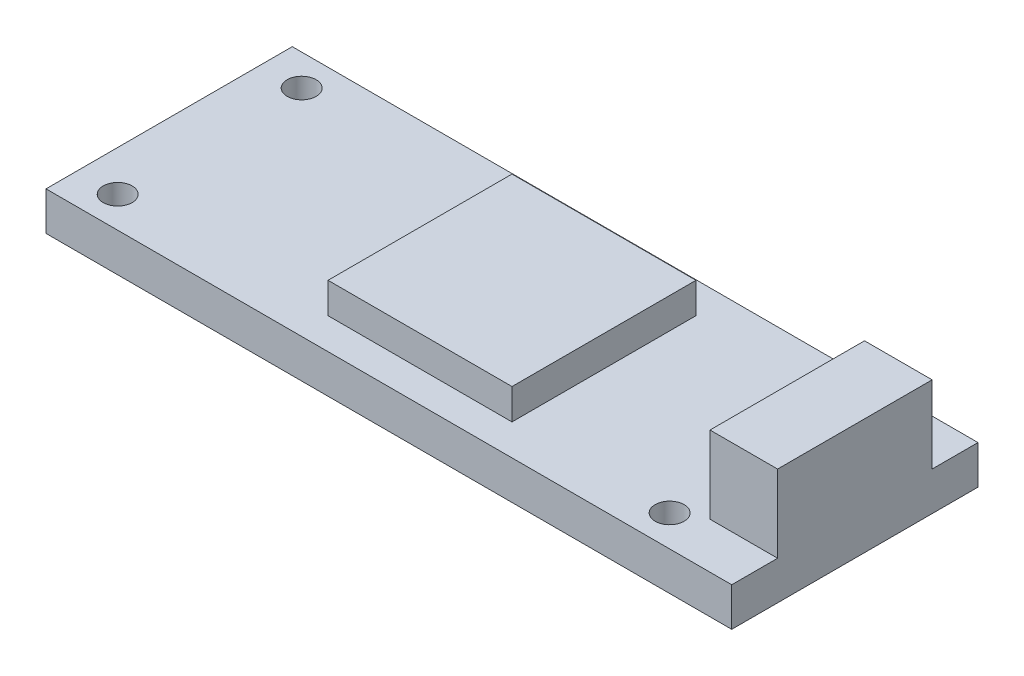
SolidWorks part; units mm, degrees
ref_plane "Front Plane" through (0, 0, 0) normal (0, 0, 1) x (1, 0, 0)
ref_plane "Top Plane" through (0, 0, 0) normal (0, 1, 0) x (1, 0, 0)
ref_plane "Right Plane" through (0, 0, 0) normal (1, 0, 0) x (0, 0, -1)
sketch "Sketch1" plane through (0, 0, 0) normal (0, 1, 0) x (1, 0, 0)
  line L1 (-35.5, -12.75) -> (35.5, -12.75)
  line L2 (-35.5, -12.75) -> (-35.5, 12.75)
  line L3 (-35.5, 12.75) -> (35.5, 12.75)
  line L4 (35.5, -12.75) -> (35.5, 12.75)
  line L5 (-35.5, -12.75) -> (35.5, 12.75) construction
  line L6 (-35.5, 12.75) -> (35.5, -12.75) construction
  point P0 (0, 0)
  dimension "D1" = 71
  dimension "D2" = 25.5
extrude "Boss-Extrude2" add sketch "Sketch1" along normal blind 4
sketch "Sketch4" plane through (0, 4, 0) normal (0, 1, 0) x (1, 0, 0)
  line L0 (-35.5, 0) -> (35.5, 0) construction
  line L1 (35.5, -12.75) -> (35.5, 12.75) construction
  line L3 (28.5, -8) -> (35.5, -8)
  line L4 (28.5, -8) -> (28.5, 8)
  line L5 (28.5, 8) -> (35.5, 8)
  line L6 (35.5, -8) -> (35.5, 8)
  line L7 (28.5, -8) -> (35.5, 8) construction
  line L8 (28.5, 8) -> (35.5, -8) construction
  point P0 (32, 0)
  point P6 (0, 0)
  dimension "D1" = 16
  dimension "D2" = 7
extrude "Boss-Extrude3" add sketch "Sketch4" along normal blind 8
sketch "Sketch5" plane through (0, 4, 0) normal (0, 1, 0) x (1, 0, 0)
  line L1 (-9.525, -9.525) -> (9.525, -9.525)
  line L2 (-9.525, -9.525) -> (-9.525, 9.525)
  line L3 (-9.525, 9.525) -> (9.525, 9.525)
  line L4 (9.525, -9.525) -> (9.525, 9.525)
  line L5 (-9.525, -9.525) -> (9.525, 9.525) construction
  line L6 (-9.525, 9.525) -> (9.525, -9.525) construction
  point P0 (0, 0)
  dimension "D1" = 19.05
  dimension "D2" = 19.05
extrude "Boss-Extrude4" add sketch "Sketch5" along normal blind 3.174
sketch "Sketch6" plane through (0, 4, 0) normal (0, 1, 0) x (1, 0, 0)
  line L1 (-31.302, -9.525) -> (25.848, -9.525) construction
  line L2 (-31.302, -9.525) -> (-31.302, 9.525) construction
  line L3 (-31.302, 9.525) -> (25.848, 9.525) construction
  line L4 (25.848, -9.525) -> (25.848, 9.525) construction
  line L5 (-31.302, -9.525) -> (25.848, 9.525) construction
  line L6 (-31.302, 9.525) -> (25.848, -9.525) construction
  line L7 (35.5, -12.75) -> (35.5, 12.75) construction
  circle A0 centre (-31.302, 9.525) radius 1.5
  circle A1 centre (-31.302, -9.525) radius 1.5
  circle A2 centre (25.848, 9.525) radius 1.5
  circle A3 centre (25.848, -9.525) radius 1.5
  point P0 (-2.727, 0)
  dimension "D4" = 3
  dimension "D5" = 3
  dimension "D6" = 3
  dimension "D1" = 57.15
  dimension "D2" = 19.05
  dimension "D3" = 9.652
extrude "Cut-Extrude1" cut sketch "Sketch6" against normal through all
